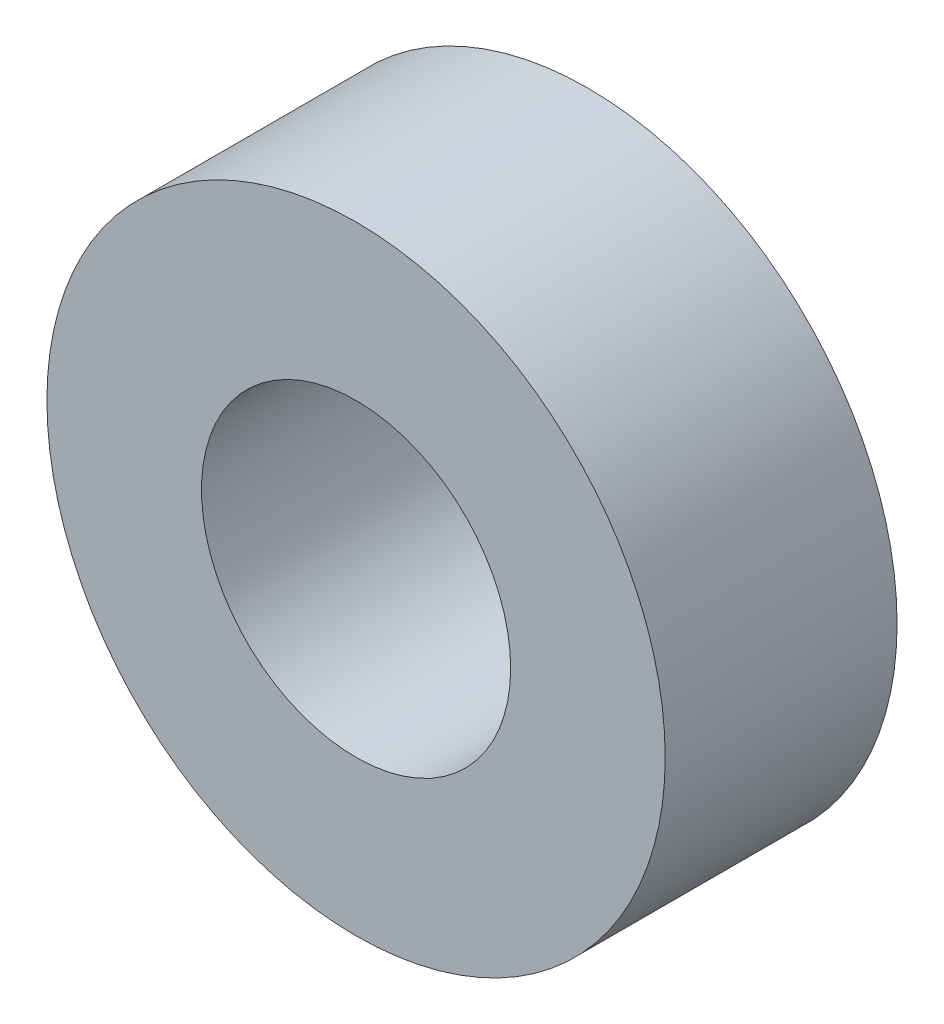
SolidWorks part; units mm, degrees
material "Delrin 2700 NC010, Low Viscosity Acetal Copolymer (SS)"
ref_plane "Front Plane" through (0, 0, 0) normal (0, 0, 1) x (1, 0, 0)
ref_plane "Top Plane" through (0, 0, 0) normal (0, 1, 0) x (1, 0, 0)
ref_plane "Right Plane" through (0, 0, 0) normal (1, 0, 0) x (0, 0, -1)
sketch "Sketch1" plane through (0, 0, 0) normal (0, 0, 1) x (1, 0, 0)
  circle A0 centre (0, 0) radius 12.7
  circle A1 centre (0, 0) radius 25.4
  dimension "D1" = 25.4
  dimension "D2" = 12.7
extrude "Boss-Extrude1" add sketch "Sketch1" along normal mid plane 19.05
